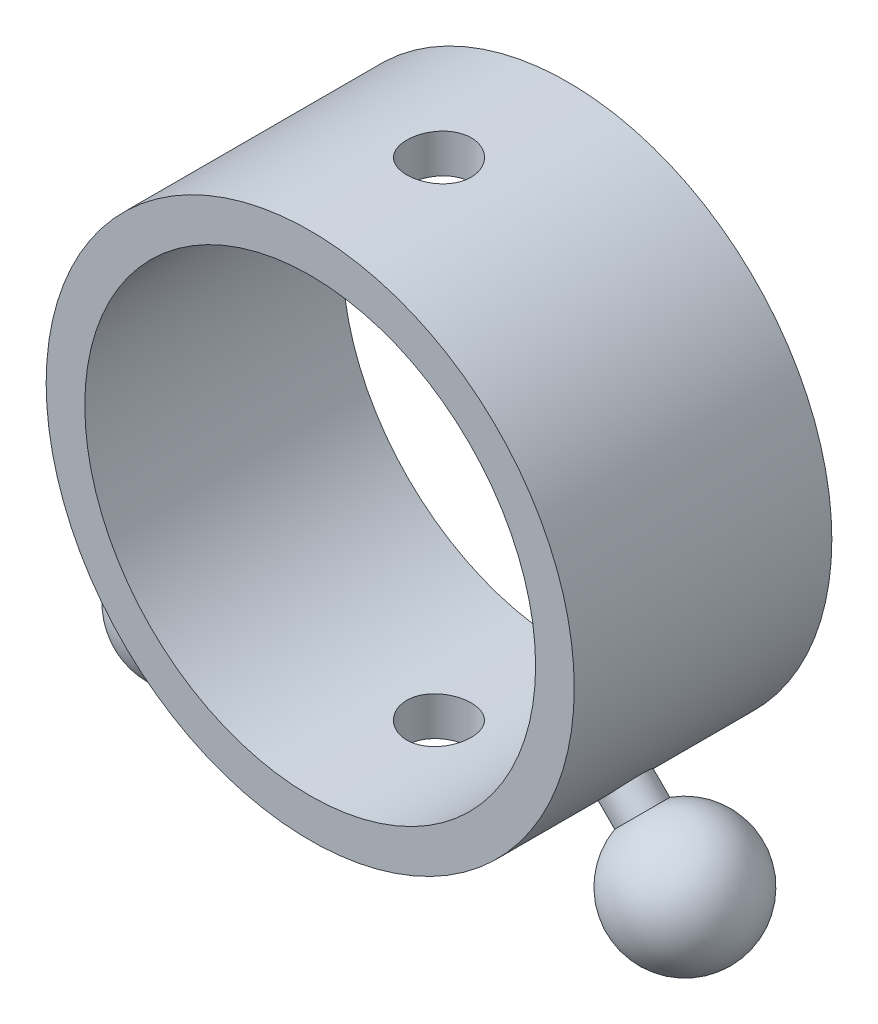
SolidWorks part; units mm, degrees
material "1060 Alloy"
ref_plane "Front Plane" through (0, 0, 0) normal (0, 0, 1) x (1, 0, 0)
ref_plane "Top Plane" through (0, 0, 0) normal (0, 1, 0) x (1, 0, 0)
ref_plane "Right Plane" through (0, 0, 0) normal (1, 0, 0) x (0, 0, -1)
sketch "Sketch1" plane through (0, 0, 0) normal (0, 0, 1) x (1, 0, 0)
  line L0 (0, 17.5) -> (0, 20.5) construction
  circle A0 centre (0, 0) radius 20.5
  circle A1 centre (0, 0) radius 17.5
  dimension "D1" = 35
  dimension "D2" = 3
extrude "Boss-Extrude1" add sketch "Sketch1" along normal blind 20
sketch "Sketch2" plane through (0, 0, 0) normal (0, 1, 0) x (1, 0, 0)
  line L0 (0, 0) -> (0, -20) construction
  line L1 (-20.5, -20) -> (20.5, -20) construction
  circle A0 centre (0, -10) radius 2.5
  dimension "D1" = 5
extrude "Cut-Extrude1" cut sketch "Sketch2" against normal through all both and the other way through all contours A0
ref_plane "Plane1" through (14.4957, -14.4957, 0) normal (-0.7071, 0.7071, 0) x (0, 0, -1)
ref_plane "Plane2" through (0, 0, 10) normal (0, 0, -1) x (-1, 0, 0)
sketch "Sketch4" plane through (0, 0, 10) normal (0, 0, -1) x (-1, 0, 0)
  line L0 (0, 0) -> (22.6274, -22.6274) construction
  line L1 (0, 0) -> (0, -17.5) construction
  line L5 (14.1421, -14.1421) -> (22.6274, -22.6274)
  line L6 (14.5425, -17.0174) -> (12.9047, -15.3796)
  line L7 (12.9047, -15.3796) -> (14.1421, -14.1421)
  circle A0 centre (0, 0) radius 17.5 construction
  circle A1 centre (0, 0) radius 20.5 construction
  arc A3 (22.6274, -22.6274) -> (14.5425, -17.0174) centre (19.0919, -19.0919) cw
  point P8 (14.1421, -14.1421)
  point P13 (14.4957, -14.4957)
  dimension "D5" = 5
  dimension "D1" = 45
  dimension "D2" = 12
  dimension "D3" = 0.5
  dimension "D4" = 1.75
revolve "Revolve1" add sketch "Sketch4" angle 360 about L5
mirror "Mirror1" about plane through (0, 0, 0) normal (1, 0, 0) of "Revolve1"
ref_plane "Plane3" through (0, 0, 10) normal (0, 0, -1) x (-1, 0, 0)
sketch "Sketch6" plane through (0, 0, 10) normal (0, 0, -1) x (-1, 0, 0)
  arc A0 (14.5425, -17.0174) -> (17.0174, -14.5425) centre (19.0919, -19.0919) ccw construction
  arc A1 (-17.0174, -14.5425) -> (-14.5425, -17.0174) centre (-19.0919, -19.0919) ccw construction
  point P0 (19.0919, -19.0919)
  point P6 (-19.0919, -19.0919)
equation "\"frontTubeLength\"= 1200mm"
equation "\"outDiameter\"= 35mm"
equation "\"keelOutDiameter\"= 1in"
equation "\"bottomTubeLength\"= \"frontTubeLength\"*0.9"
equation "\"frontShaftDiameter\"= 20mm"
equation "\"D1@Sketch1\"=\"outDiameter\""
equation "\"boltDiameter\"= 5mm"
equation "\"D1@Sketch2\" = \"boltDiameter\""
